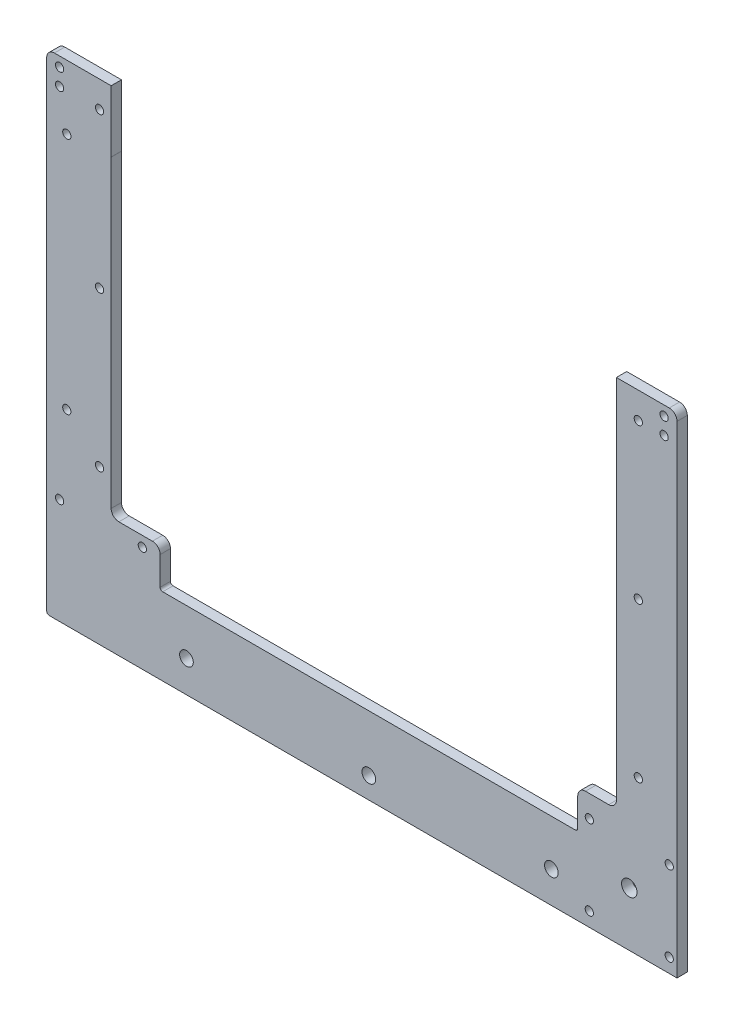
SolidWorks part; units mm, degrees
ref_plane "Plano frontal" through (0, 0, 0) normal (0, 0, 1) x (1, 0, 0)
ref_plane "Plano superior" through (0, 0, 0) normal (0, 1, 0) x (1, 0, 0)
ref_plane "Plano direito" through (0, 0, 0) normal (1, 0, 0) x (0, 0, -1)
sketch "Esboço1" plane through (0, 0, 0) normal (0, 0, 1) x (1, 0, 0)
  line L0 (-36.7564, -93.1156) -> (-55.7564, -93.1156)
  line L1 (-35.7564, -108.1156) -> (124.2436, -108.1156)
  line L2 (-55.7564, -79.1156) -> (-55.7564, 27.8844)
  line L3 (-52.7564, 30.8844) -> (141.2436, 30.8844)
  line L4 (144.2436, -79.1156) -> (144.2436, 27.8844)
  line L5 (168.2436, -138.1156) -> (-79.7564, -138.1156)
  line L6 (169.2436, -137.1156) -> (169.2436, 48.8844)
  line L7 (166.2436, 51.8844) -> (-77.7564, 51.8844)
  line L8 (-80.7564, -137.1156) -> (-80.7564, 48.8844)
  line L9 (44.2436, -142.1156) -> (44.2436, -132.526) construction
  line L10 (144.2436, -93.1156) -> (144.2436, -79.1156)
  line L11 (-36.7564, -93.1156) -> (-36.7564, -107.1156)
  line L12 (125.2436, -93.1156) -> (144.2436, -93.1156)
  line L13 (-36.7564, -93.1156) -> (-41.6564, -93.1156) construction
  line L15 (125.2436, -93.1156) -> (125.2436, -107.1156)
  line L17 (-55.7564, -93.1156) -> (-55.7564, -79.1156)
  arc A2 (141.2436, 30.8844) -> (144.2436, 27.8844) centre (141.2436, 27.8844) cw
  arc A3 (-55.7564, 27.8844) -> (-52.7564, 30.8844) centre (-52.7564, 27.8844) cw
  arc A4 (-77.7564, 51.8844) -> (-80.7564, 48.8844) centre (-77.7564, 48.8844) ccw
  arc A5 (169.2436, 48.8844) -> (166.2436, 51.8844) centre (166.2436, 48.8844) ccw
  arc A6 (-36.7564, -107.1156) -> (-35.7564, -108.1156) centre (-35.7564, -107.1156) ccw
  arc A7 (-79.7564, -138.1156) -> (-80.7564, -137.1156) centre (-79.7564, -137.1156) cw
  arc A9 (168.2436, -138.1156) -> (169.2436, -137.1156) centre (168.2436, -137.1156) ccw
  arc A12 (125.2436, -107.1156) -> (124.2436, -108.1156) centre (124.2436, -107.1156) cw
  dimension "D2" = 1
  dimension "D10" = 44
  dimension "D11" = 3
  dimension "D12" = 45
  dimension "D13" = 1
  dimension "D3" = 250
  dimension "D4" = 190
  dimension "D5" = 21
  dimension "D6" = 30
  dimension "D7" = 25
  dimension "D8" = 25
  dimension "D9" = 45
extrude "Ressalto-extrusão1" add sketch "Esboço1" along normal blind 4
hole_wizard "Furo com folga de M31" positions "Esboço3" profile "Esboço2" hole size "M3" standard "ISO" end condition through all
sketch "Esboço3" plane through (0, 0, 0) normal (0, 0, -1) x (-1, 0, 0)
  line L0 (-44.2436, 30.8844) -> (-44.2436, 180.2437) construction
  line L2 (-148.7436, -78.3479) -> (-148.7436, -20.0979) construction
  line L3 (-148.7436, -20.0979) -> (-148.7436, 41.6521) construction
  line L5 (-144.2436, -93.1156) -> (-144.2436, 27.8844) construction
  line L7 (-141.2436, 30.8844) -> (52.7564, 30.8844) construction
  point P0 (-148.7436, -78.3479)
  point P3 (-148.7436, -18.3479)
  point P6 (-148.7436, 41.6521)
  point P15 (60.2564, 41.6521)
  point P16 (60.2564, -18.3479)
  point P17 (60.2564, -78.3479)
  point P30 (72.9564, 27.0185)
  point P32 (72.9564, -65.4815)
  point P34 (19.6564, -65.4815)
  point P36 (19.6564, 27.0185)
  dimension "D1" = 4.5
sketch "Esboço2" plane through (148.7436, -78.3479, 0) normal (1, 0, 0) x (0, 1, 0)
  line L0 (0, 0) -> (0, 4)
  line L1 (0, 4) -> (1.6, 4)
  line L2 (1.6, 4) -> (1.6, 0)
  line L5 (1.6, 0) -> (0, 0)
  line L11 (0, -6.35) -> (0, 107.95) construction
  dimension "Thru Hole Dia." = 3.2
  dimension "Thru Hole Depth" = 4
fillet "Filete1" radius 3 4 edges at (144.2436, -93.1156, 2) (125.2436, -93.1156, 2) (-55.7564, -93.1156, 2) (-36.7564, -93.1156, 2)
hole_wizard "M3 Clearance Hole1" positions "Esboço11" profile "Esboço10" hole size "M3" standard "ISO" end condition through all
sketch "Esboço11" plane through (0, 0, 0) normal (0, 0, -1) x (-1, 0, 0)
  point P0 (-164.23, -97.103)
  point P12 (43.67, -97.103)
  point P15 (75.7428, -97.103)
sketch "Esboço10" plane through (164.23, -97.103, 0) normal (1, 0, 0) x (0, 1, 0)
  line L0 (0, 0) -> (0, 4)
  line L1 (0, 4) -> (1.6, 4)
  line L2 (1.6, 4) -> (1.6, 0)
  line L5 (1.6, 0) -> (0, 0)
  line L11 (0, -6.35) -> (0, 107.95) construction
  dimension "Thru Hole Dia." = 3.2
  dimension "Thru Hole Depth" = 4
sketch "Esboço16" plane through (0, 0, 4) normal (0, 0, 1) x (1, 0, 0)
  line L0 (150.0557, -138.1156) -> (169.2436, -138.1156) construction
  line L3 (-79.7564, -138.1156) -> (168.2436, -138.1156) construction
  line L5 (169.2436, -137.1156) -> (169.2436, 48.8844) construction
  line L6 (169.2436, -127.14) -> (169.2436, -138.1156) construction
hole_wizard "Furo com folga de M32" positions "Esboço19" profile "Esboço18" hole size "M3" standard "Ansi Metric" end condition through all
sketch "Esboço19" plane through (0, 0, 4) normal (0, 0, 1) x (1, 0, 0)
  point P14 (44.2436, 46.9871)
sketch "Esboço18" plane through (44.2436, 46.9871, 4) normal (1, 0, 0) x (0, -1, 0)
  line L0 (0, 0) -> (0, 4)
  line L1 (0, 4) -> (1.435, 4)
  line L2 (1.435, 4) -> (1.435, 0)
  line L5 (1.435, 0) -> (0, 0)
  line L11 (0, -6.35) -> (0, 107.95) construction
  dimension "Thru Hole Dia." = 2.87
  dimension "Thru Hole Depth" = 4
hole_wizard "M3 Clearance Hole2" positions "Sketch2" profile "Sketch1" hole size "M3" standard "ISO" end condition through all
sketch "Sketch2" plane through (0, 0, 4) normal (0, 0, 1) x (1, 0, 0)
  point P0 (161.5603, 35.4802)
  point P3 (161.5603, 4.4802)
sketch "Sketch1" plane through (161.5603, 35.4802, 4) normal (1, 0, 0) x (0, -1, 0)
  line L0 (0, 0) -> (0, 4)
  line L1 (0, 4) -> (1.6, 4)
  line L2 (1.6, 4) -> (1.6, 0)
  line L5 (1.6, 0) -> (0, 0)
  line L11 (0, -6.35) -> (0, 107.95) construction
  dimension "Thru Hole Dia." = 3.2
  dimension "Thru Hole Depth" = 4
sketch "Sketch3" plane through (0, 0, 4) normal (0, 0, 1) x (1, 0, 0)
  line L3 (44.2436, 30.8844) -> (44.2436, 18.6097) construction
  line L8 (141.2436, 30.8844) -> (-52.7564, 30.8844) construction
  line L9 (183.6742, -138.1156) -> (156.2436, -138.1156)
  line L10 (183.6742, 51.8844) -> (183.6742, -138.1156)
  line L11 (156.2436, 51.8844) -> (183.6742, 51.8844)
  line L12 (156.2436, -138.1156) -> (156.2436, 51.8844)
extrude "Cut-Extrude1" cut sketch "Sketch3" against normal blind 10
sketch "Sketch5" plane through (0, 0, 0) normal (0, 0, -1) x (-1, 0, 0)
  line L0 (-44.2436, 30.8844) -> (-44.2436, 20.8984) construction
  line L1 (-141.2436, 30.8844) -> (52.7564, 30.8844) construction
  line L2 (-145.2403, -97.5002) -> (-140.2436, -97.5002)
  line L3 (-145.2403, 30.8844) -> (-145.2403, -97.5002)
  line L4 (-141.2436, 30.8844) -> (52.7564, 30.8844) construction
  line L6 (-137.2442, 30.8844) -> (-145.2403, 30.8844)
  line L10 (-140.2436, 27.9415) -> (-140.2436, -97.5002)
  arc A0 (-137.2442, 30.8844) -> (-140.2436, 27.9415) centre (-137.2442, 27.8844) ccw
  dimension "D1" = 3
extrude "Boss-Extrude1" add sketch "Sketch5" against normal blind 4
fillet "Fillet3" radius 3 1 edges at (156.2436, 51.8844, 2)
sketch "Sketch10" plane through (0, 0, 0) normal (0, 0, -1) x (-1, 0, 0)
  line L0 (-156.2436, -138.1156) -> (-156.2436, 48.8844)
  line L1 (-156.2436, -138.1156) -> (-163.7436, -138.1156)
  line L4 (-150.0557, -138.1156) -> (-169.2436, -138.1156) construction
  line L6 (-163.7436, -138.1156) -> (-163.7436, 51.8844)
  line L10 (-163.7436, 51.8844) -> (-153.2436, 51.8844)
  arc A1 (-153.2436, 51.8844) -> (-156.2436, 48.8844) centre (-153.2436, 48.8844) ccw
extrude "Boss-Extrude3" add sketch "Sketch10" against normal blind 4
hole_wizard "M3 Clearance Hole4" positions "Sketch12" profile "Sketch11" hole size "M3" standard "ISO" end condition through all
sketch "Sketch12" plane through (0, 0, 0) normal (0, 0, -1) x (-1, 0, 0)
  point P0 (-160.7436, -101.6156)
  point P2 (-160.7436, -132.6156)
  point P5 (-129.7436, -132.6156)
  point P6 (-129.7436, -101.6156)
sketch "Sketch11" plane through (160.7436, -101.6156, 0) normal (1, 0, 0) x (0, 1, 0)
  line L0 (0, 0) -> (0, 4)
  line L1 (0, 4) -> (1.6, 4)
  line L2 (1.6, 4) -> (1.6, 0)
  line L5 (1.6, 0) -> (0, 0)
  line L11 (0, -6.35) -> (0, 107.95) construction
  dimension "Thru Hole Dia." = 3.2
  dimension "Thru Hole Depth" = 4
fillet "Fillet5" radius 3 2 edges at (163.7436, 51.8844, 2) (140.2436, -93.1156, 2)
hole_wizard "M5 Clearance Hole1" positions "Esboço15" profile "Esboço14" hole size "M5" standard "ISO" end condition through all
sketch "Esboço15" plane through (0, 0, 0) normal (0, 0, -1) x (-1, 0, 0)
  point P1 (-115.0336, -125.8856)
  point P3 (26.5464, -125.8856)
  point P4 (-44.1899, -129.8656)
sketch "Esboço14" plane through (115.0336, -125.8856, 0) normal (1, 0, 0) x (0, 1, 0)
  line L0 (0, 0) -> (0, 4)
  line L1 (0, 4) -> (2.65, 4)
  line L2 (2.65, 4) -> (2.65, 0)
  line L5 (2.65, 0) -> (0, 0)
  line L11 (0, -6.35) -> (0, 107.95) construction
  dimension "Thru Hole Dia." = 5.3
  dimension "Thru Hole Depth" = 4
sketch "Sketch15" plane through (0, 0, 0) normal (0, 0, -1) x (-1, 0, 0)
  circle A1 centre (-145.2436, -117.1156) radius 3
  point P0 (-145.2436, -117.1156)
  point P2 (-144.7712, -129.7569)
  point P4 (-145.2436, -117.1156)
  point P5 (-144.7712, -129.7569)
  dimension "D1" = 6
extrude "Cut-Extrude6" cut sketch "Sketch15" against normal through all
sketch "Sketch17" plane through (0, 0, 0) normal (0, 0, -1) x (-1, 0, 0)
  line L1 (-140.2436, 27.9415) -> (55.7564, 27.9415)
  line L2 (-140.2436, 27.9415) -> (-140.2436, 51.8844)
  line L3 (-140.2436, 51.8844) -> (55.7564, 51.8844)
  line L4 (55.7564, 27.9415) -> (55.7564, 51.8844)
extrude "Cut-Extrude8" cut sketch "Sketch17" against normal blind 5
hole_wizard "M3 Clearance Hole5" positions "Sketch21" profile "Sketch18" hole size "M3" standard "ISO" end condition through all
sketch "Sketch21" plane through (0, 0, 4) normal (0, 0, 1) x (1, 0, 0)
  line L0 (-80.7564, 48.8844) -> (-80.7564, -137.1156) construction
  line L1 (163.7436, 48.8844) -> (163.7436, -138.1156) construction
  line L2 (-60.2564, 41.6521) -> (158.7436, 41.6521) construction
  point P0 (-75.7564, 41.6521)
  point P2 (-75.7564, 48.1521)
  point P4 (158.7436, 48.1521)
  point P6 (158.7436, 41.6521)
  dimension "D1" = 5
  dimension "D2" = 5
  dimension "D3" = 6.5
  dimension "D4" = 5
  dimension "D5" = 5
  dimension "D6" = 6.5
sketch "Sketch18" plane through (-75.7564, 41.6521, 4) normal (1, 0, 0) x (0, -1, 0)
  line L0 (0, 0) -> (0, 4)
  line L1 (0, 4) -> (1.6, 4)
  line L2 (1.6, 4) -> (1.6, 0)
  line L5 (1.6, 0) -> (0, 0)
  line L11 (0, -6.35) -> (0, 107.95) construction
  dimension "Thru Hole Dia." = 3.2
  dimension "Thru Hole Depth" = 4
sketch "Sketch22" plane through (0, 0, 0) normal (0, 0, -1) x (-1, 0, 0)
  line L0 (-44.1899, -129.8656) -> (-44.1899, -123.2156) construction
  line L2 (-46.8408, -129.8656) -> (-46.8408, -123.2156)
  line L3 (-41.539, -129.8656) -> (-41.539, -123.2156)
  arc A0 (-46.8408, -129.8656) -> (-41.539, -129.8656) centre (-44.1899, -129.8656) ccw
  arc A1 (-41.539, -123.2156) -> (-46.8408, -123.2156) centre (-44.1899, -123.2156) ccw
  point P5 (-44.1899, -126.5406)
extrude "Cut-Extrude9" [suppressed] cut sketch "Sketch22" against normal blind 4
